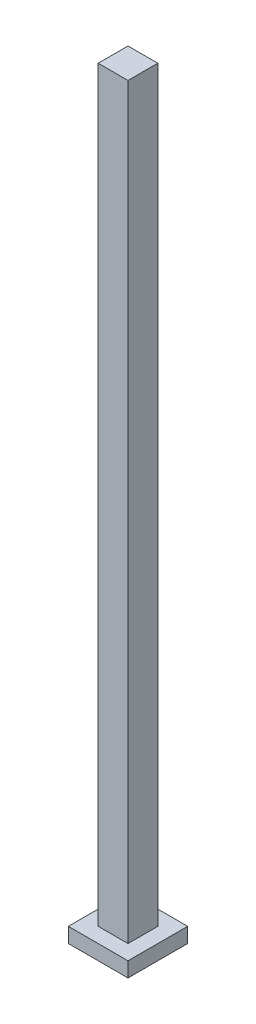
SolidWorks part; units mm, degrees
ref_plane "Piano frontale" through (0, 0, 0) normal (0, 0, 1) x (1, 0, 0)
ref_plane "Piano superiore" through (0, 0, 0) normal (0, 1, 0) x (1, 0, 0)
ref_plane "Piano destro" through (0, 0, 0) normal (1, 0, 0) x (0, 0, -1)
sketch "Schizzo1" plane through (0, 0, 0) normal (0, 0, 1) x (1, 0, 0)
  line L0 (0, 0) -> (100, 0)
  line L1 (100, 0) -> (100, 50)
  line L2 (100, 50) -> (-100, 50)
  line L3 (-100, 50) -> (-100, 0)
  line L4 (-100, 0) -> (0, 0)
  dimension "D1" = 200
  dimension "D2" = 50
extrude "Estrusione-Estrusione1" add sketch "Schizzo1" along normal mid plane 200
sketch "Schizzo2" plane through (0, 50, 0) normal (0, 1, 0) x (1, 0, 0)
  line L1 (-50, 50) -> (50, 50)
  line L2 (-50, 50) -> (-50, -50)
  line L3 (-50, -50) -> (50, -50)
  line L4 (50, 50) -> (50, -50)
  line L5 (-45.2727, 44.599) -> (44.7273, 44.599)
  line L6 (-45.2727, 44.599) -> (-45.2727, -45.401)
  line L7 (-45.2727, -45.401) -> (44.7273, -45.401)
  line L8 (44.7273, 44.599) -> (44.7273, -45.401)
  dimension "D1" = 100
  dimension "D2" = 100
  dimension "D3" = 50
  dimension "D4" = 50
  dimension "D5" = 90
  dimension "D6" = 90
extrude "Estrusione-Estrusione2" add sketch "Schizzo2" along normal blind 2500
sketch "Schizzo3" plane through (0, 2550, 0) normal (0, 1, 0) x (1, 0, 0)
  line L1 (-50, 50) -> (50, 50)
  line L2 (-50, 50) -> (-50, -50)
  line L3 (-50, -50) -> (50, -50)
  line L4 (50, 50) -> (50, -50)
extrude "Estrusione-Estrusione3" add sketch "Schizzo3" along normal blind 5 contours L3 L4 L1 L2
